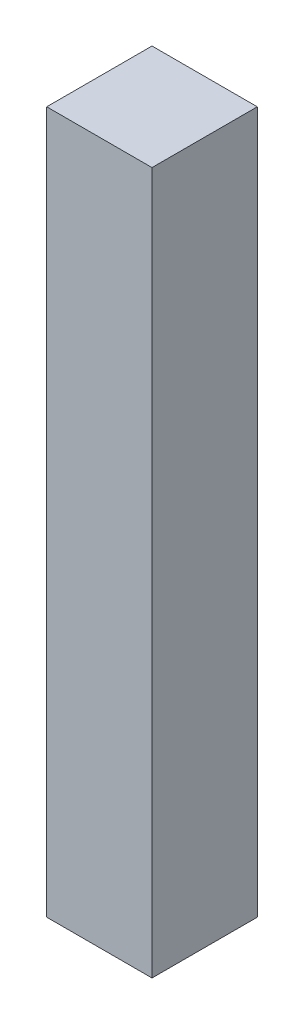
SolidWorks part; units mm, degrees
ref_plane "Ebene vorne" through (0, 0, 0) normal (0, 0, 1) x (1, 0, 0)
ref_plane "Ebene oben" through (0, 0, 0) normal (0, 1, 0) x (1, 0, 0)
ref_plane "Ebene rechts" through (0, 0, 0) normal (1, 0, 0) x (0, 0, -1)
sketch "Sketch1" plane through (0, 0, 0) normal (0, 1, 0) x (1, 0, 0)
  line L1 (-30, -30) -> (30, -30)
  line L2 (-30, -30) -> (-30, 30)
  line L3 (-30, 30) -> (30, 30)
  line L4 (30, -30) -> (30, 30)
  line L5 (-30, -30) -> (30, 30) construction
  line L6 (-30, 30) -> (30, -30) construction
  point P0 (0, 0)
  dimension "D1" = 60
  dimension "D2" = 60
extrude "Boss-Extrude1" add sketch "Sketch1" along normal blind 400
